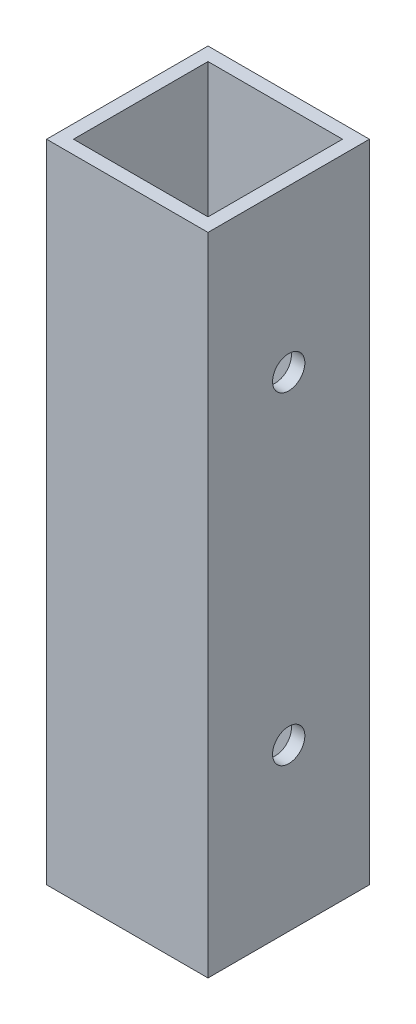
SolidWorks part; units mm, degrees
ref_plane "Front Plane" through (0, 0, 0) normal (0, 0, 1) x (1, 0, 0)
ref_plane "Top Plane" through (0, 0, 0) normal (0, 1, 0) x (1, 0, 0)
ref_plane "Right Plane" through (0, 0, 0) normal (1, 0, 0) x (0, 0, -1)
sketch "Sketch1" plane through (0, 0, 0) normal (0, 1, 0) x (1, 0, 0)
  line L0 (-20.955, 0) -> (20.955, 0) construction
  line L1 (-15.875, 15.875) -> (15.875, 15.875)
  line L2 (-15.875, 15.875) -> (-15.875, -15.875)
  line L3 (-15.875, -15.875) -> (15.875, -15.875)
  line L4 (15.875, 15.875) -> (15.875, -15.875)
  line L5 (0, -20.955) -> (0, 20.955) construction
  line L6 (-19.05, 19.05) -> (19.05, 19.05)
  line L7 (19.05, 19.05) -> (19.05, -19.05)
  line L8 (-19.05, -19.05) -> (19.05, -19.05)
  line L9 (-19.05, 19.05) -> (-19.05, -19.05)
  dimension "D1" = 31.75
  dimension "D2" = 31.75
  dimension "D3" = 15.875
  dimension "D4" = 15.875
  dimension "D5" = 3.175
extrude "Boss-Extrude1" add sketch "Sketch1" along normal blind 152.4
sketch "Sketch2" plane through (-19.05, 0, 0) normal (-1, 0, 0) x (0, 0, 1)
  line L0 (0, -20.955) -> (0, 20.955) construction
  line L1 (20.955, 0) -> (-20.955, 0) construction
  line L2 (-19.05, 152.4) -> (19.05, 152.4) construction
  circle A0 centre (0, 114.3) radius 3.81
  circle A1 centre (0, 38.1) radius 3.81
  dimension "D3" = 7.62
  dimension "D1" = 38.1
  dimension "D2" = 38.1
extrude "Cut-Extrude1" cut sketch "Sketch2" against normal blind 152.4
